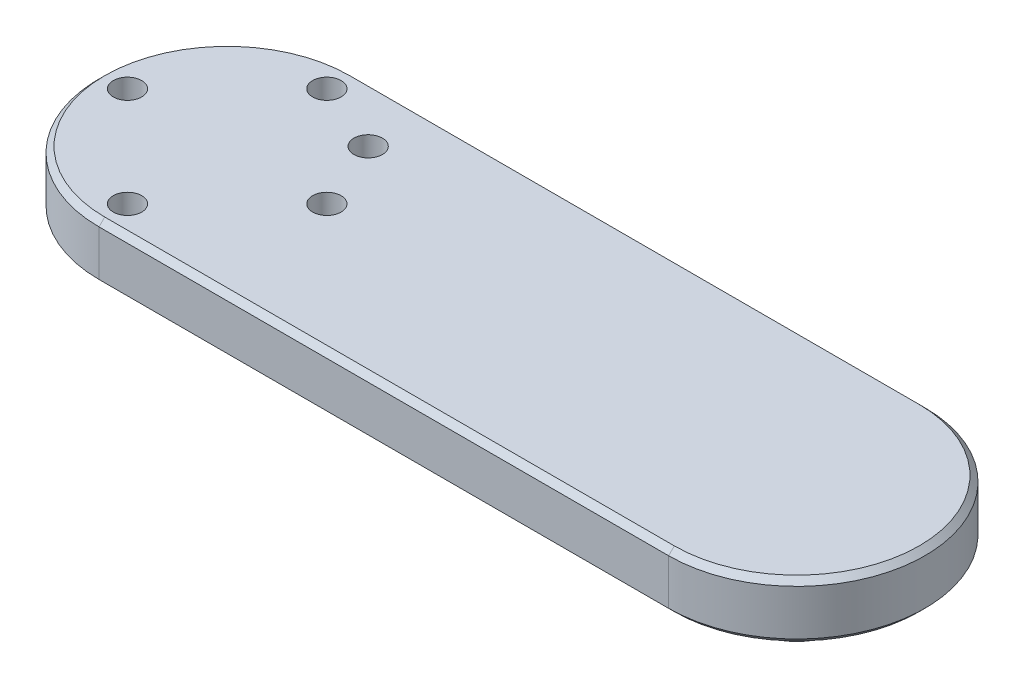
SolidWorks part; units mm, degrees
ref_plane "Front Plane" through (0, 0, 0) normal (0, 0, 1) x (1, 0, 0)
ref_plane "Top Plane" through (0, 0, 0) normal (0, 1, 0) x (1, 0, 0)
ref_plane "Right Plane" through (0, 0, 0) normal (1, 0, 0) x (0, 0, -1)
sketch "Sketch1" plane through (0, 0, 0) normal (0, 1, 0) x (1, 0, 0)
  line L0 (0, 45) -> (0, 168.956) construction
  line L1 (-100, 45) -> (100, 45)
  line L2 (100, -45) -> (-100, -45)
  arc A0 (-100, 45) -> (-100, -45) centre (-100, 0) ccw
  arc A1 (100, 45) -> (100, -45) centre (100, 0) cw
  dimension "D1" = 90
  dimension "D2" = 100
extrude "Boss-Extrude1" add sketch "Sketch1" along normal blind 20
sketch "Sketch2" plane through (0, 20, 0) normal (0, 1, 0) x (1, 0, 0)
  circle A0 centre (-135, 0) radius 5
  arc A1 (-100, 45) -> (-100, -45) centre (-100, 0) ccw construction
  circle A2 centre (-100, 35) radius 5
  circle A3 centre (-65, 0) radius 5
  circle A4 centre (-100, -35) radius 5
  circle A5 centre (-75.2513, 24.7487) radius 5
  point P14 (-100, 0)
  dimension "D1" = 10
  dimension "D4" = 10
  dimension "D2" = 35
  dimension "D5" = 35
  dimension "D6" = 45
  dimension "D3" = 4
extrude "Cut-Extrude1" cut sketch "Sketch2" against normal through all
sketch "Sketch3" plane through (0, 0, 0) normal (0, -1, 0) x (1, 0, 0)
  circle A0 centre (100, 0) radius 15
  dimension "D1" = 30
extrude "Boss-Extrude2" add sketch "Sketch3" along normal blind 20
chamfer "Chamfer1" distance 2 angle 45 8 edges at (0, 20, -45) (-145, 20, 0) (145, 20, 0) (0, 20, 45) (0, 0, -45) (-145, 0, 0) (145, 0, 0) (0, 0, 45)
